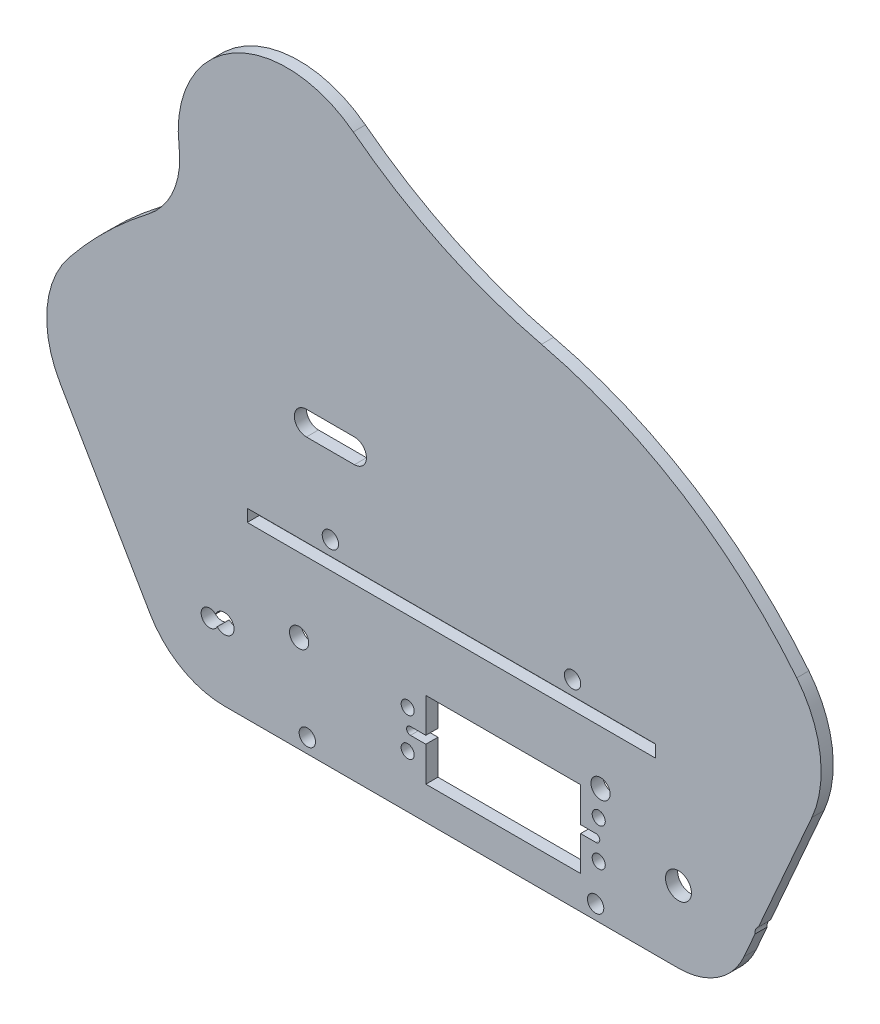
SolidWorks part; units mm, degrees
ref_plane "Front Plane" through (0, 0, 0) normal (0, 0, 1) x (1, 0, 0)
ref_plane "Top Plane" through (0, 0, 0) normal (0, 1, 0) x (1, 0, 0)
ref_plane "Right Plane" through (0, 0, 0) normal (1, 0, 0) x (0, 0, -1)
sketch "Sketch1" plane through (0, 0, 0) normal (0, 0, 1) x (1, 0, 0)
  line L8 (0, 18.9078) -> (120.015, 18.9078) construction
  line L18 (155.2575, 52.1157) -> (-50.9787, 52.1157) construction
  line L37 (0, 0) -> (120.015, 0)
  line L42 (19.7347, 25.5664) -> (0, 18.9078) construction
  line L55 (60.0075, 18.9078) -> (60.0075, 0) construction
  line L60 (137.3256, 11.3022) -> (120.015, 0) construction
  line L61 (-19.6481, 11.3022) -> (0, 0) construction
  line L62 (155.2575, 52.1157) -> (137.3256, 11.3022)
  line L63 (-43.3855, 52.1157) -> (-19.6481, 11.3022)
  line L64 (155.2575, 52.1157) -> (-43.3855, 52.1157) construction
  line L65 (137.3256, 11.3022) -> (-19.6481, 11.3022) construction
  line L66 (120.015, 18.9078) -> (99.4008, 30.8094) construction
  line L67 (151.2687, 82.096) -> (-41.1067, 82.096) construction
  circle A21 centre (120.015, 18.9078) radius 3.429
  circle A22 centre (0, 18.9078) radius 2.54
  arc A25 (137.3256, 11.3022) -> (120.015, 0) centre (120.015, 18.9078) cw
  circle A27 centre (19.7347, 25.5664) radius 2.54
  arc A34 (-19.6481, 11.3022) -> (0, 0) centre (0, 22.7296) ccw
  arc A36 (151.2687, 82.096) -> (155.2575, 52.1157) centre (128.6061, 63.8253) cw
  arc A37 (-41.1067, 82.096) -> (-43.3855, 52.1157) centre (-20.4591, 65.4498) ccw
  circle A38 centre (99.4008, 30.8094) radius 2.54
  arc A39 (151.2687, 82.096) -> (-41.1067, 82.096) centre (55.081, 4.5491) ccw
  dimension "D5" = 18.9078
  dimension "D8" = 59.818
  dimension "D3" = 20.6736
  dimension "D11" = 52.1157
  dimension "D13" = 30
  dimension "D10" = 5.08
  dimension "D15" = 123.554
  dimension "D16" = 6.858
  dimension "D4" = 18.645
  dimension "D6" = 20.8278
  dimension "D7" = 120.015
  dimension "D9" = 29.9803
  dimension "D12" = 52.1157
  dimension "D14" = 23.8032
extrude "Boss-Extrude1" add sketch "Sketch1" along normal blind 3.2004
sketch "Sketch2" plane through (0, 0, 0) normal (0, 0, -1) x (-1, 0, 0)
  line L0 (-60.0075, 52.1157) -> (-60.0075, 18.9078) construction
  line L1 (-155.2575, 52.1157) -> (50.9787, 52.1157) construction
  line L14 (0, 18.9078) -> (-120.015, 18.9078) construction
  line L15 (-60.0075, 7.62) -> (-60.0075, 0) construction
  line L28 (-92.0115, 52.1157) -> (-76.0095, 52.1157) construction
  line L29 (-76.0095, 52.1157) -> (-44.0055, 52.1157) construction
  line L30 (-44.0055, 52.1157) -> (-28.0035, 52.1157) construction
  line L31 (-98.1075, 3.81) -> (-21.9075, 3.81) construction
  line L32 (0, 0) -> (-120.015, 0) construction
  circle A0 centre (-92.0115, 52.1157) radius 2.159
  circle A3 centre (-28.0035, 52.1157) radius 2.159
  circle A4 centre (-98.1075, 3.81) radius 2.159
  circle A6 centre (-21.9075, 3.81) radius 2.159
  point P11 (-36.0045, 52.1157)
  point P16 (-84.0105, 52.1157)
  point P17 (-60.0075, 3.81)
  dimension "D3" = 4.318
  dimension "D5" = 7.62
  dimension "D1" = 76.2
  dimension "D2" = 16.002
  dimension "D4" = 48.006
extrude "Cut-Extrude1" cut sketch "Sketch2" against normal blind 3.2004
sketch "Sketch5" plane through (0, 0, 0) normal (0, 0, -1) x (-1, 0, 0)
  line L0 (0, 18.9078) -> (-120.015, 18.9078) construction
  line L6 (-94.129, 29.0678) -> (-94.129, 8.7478)
  line L7 (-53.235, 29.0678) -> (-53.235, 8.7478)
  line L12 (-73.682, 29.0678) -> (-73.682, 8.7478) construction
  line L13 (-98.932, 13.9078) -> (-98.932, 23.9078) construction
  line L14 (-48.432, 13.9078) -> (-48.432, 23.9078) construction
  line L15 (-98.932, 18.9078) -> (-48.432, 18.9078) construction
  line L21 (-94.129, 8.7478) -> (-53.235, 8.7478)
  line L25 (-94.129, 29.0678) -> (-53.235, 29.0678)
  circle A0 centre (-98.932, 23.9078) radius 1.7272
  circle A1 centre (-48.432, 13.9078) radius 1.7272
  circle A2 centre (-48.432, 23.9078) radius 1.7272
  circle A3 centre (-98.932, 13.9078) radius 1.7272
  circle A8 centre (-120.015, 18.9078) radius 3.429 construction
  point P8 (-63.635, 18.9078)
  point P9 (-73.682, 18.9078)
  dimension "D2" = 3.4544
  dimension "D3" = 40.894
  dimension "D5" = 10.4
  dimension "D6" = 46.333
  dimension "D1" = 50.5
  dimension "D4" = 20.32
extrude "Cut-Extrude3" cut sketch "Sketch5" against normal through all
sketch "Sketch6" plane through (0, 0, 3.2004) normal (0, 0, 1) x (1, 0, 0)
  line L3 (98.932, 18.9078) -> (48.432, 18.9078) construction
  line L4 (49.171, 19.9238) -> (53.235, 19.9238)
  line L5 (49.171, 19.9238) -> (49.171, 17.8918) construction
  line L7 (49.171, 17.8918) -> (53.235, 17.8918)
  line L8 (53.235, 19.9238) -> (53.235, 17.8918)
  line L9 (94.129, 19.9238) -> (98.193, 19.9238)
  line L10 (94.129, 19.9238) -> (94.129, 17.8918)
  line L11 (94.129, 17.8918) -> (98.193, 17.8918)
  line L12 (98.193, 19.9238) -> (98.193, 17.8918) construction
  line L13 (53.235, 8.7478) -> (53.235, 29.0678) construction
  line L14 (94.129, 29.0678) -> (94.129, 8.7478) construction
  arc A6 (98.193, 19.9238) -> (98.193, 17.8918) centre (98.193, 18.9078) cw
  arc A7 (49.171, 19.9238) -> (49.171, 17.8918) centre (49.171, 18.9078) ccw
  point P22 (53.235, 18.9078)
  point P23 (94.129, 18.9078)
  dimension "D4" = 4.064
  dimension "D5" = 2.032
extrude "Cut-Extrude4" cut sketch "Sketch6" against normal up to surface (3.2004 mm away) up to face at (97.2048, 23.9078, 0)
sketch "Sketch10" plane through (0, 0, 0) normal (0, 0, -1) x (-1, 0, 0)
  line L0 (0, 0) -> (-120.015, 0) construction
  line L1 (-34.3535, 78.7857) -> (-21.6535, 78.7857)
  line L2 (-34.3535, 78.7857) -> (-34.3535, 72.4357) construction
  line L3 (-34.3535, 72.4357) -> (-21.6535, 72.4357)
  line L4 (-21.6535, 78.7857) -> (-21.6535, 72.4357) construction
  arc A0 (-21.6535, 78.7857) -> (-21.6535, 72.4357) centre (-21.6535, 75.6107) cw
  arc A1 (-34.3535, 78.7857) -> (-34.3535, 72.4357) centre (-34.3535, 75.6107) ccw
  circle A4 centre (-28.0035, 52.1157) radius 2.159 construction
  dimension "D3" = 20.32
  dimension "D4" = 6.35
  dimension "D1" = 12.7
  dimension "D2" = 6.35
extrude "Cut-Extrude8" cut sketch "Sketch10" against normal up to surface (3.2004 mm away) up to face at (73.682, 18.9078, 3.2004)
sketch "Sketch11" plane through (0, 0, 0) normal (0, 0, -1) x (-1, 0, 0)
  line L5 (-76.0095, 52.1157) -> (-44.0055, 52.1157) construction
  line L7 (-60.0075, 52.1157) -> (-60.0075, 48.3057) construction
  line L9 (-6.0325, 48.3057) -> (-113.9825, 48.3057)
  line L10 (-6.0325, 48.3057) -> (-6.0325, 45.0545)
  line L11 (-6.0325, 45.0545) -> (-113.9825, 45.0545)
  line L12 (-113.9825, 48.3057) -> (-113.9825, 45.0545)
  dimension "D1" = 107.95
  dimension "D2" = 3.81
  dimension "D5" = 3.2512
extrude "Cut-Extrude9" cut sketch "Sketch11" against normal up to surface (3.2004 mm away) up to face at (28.0035, 75.6107, 3.2004)
sketch "Sketch12" plane through (0, 0, 0) normal (0, 0, -1) x (-1, 0, 0)
  circle A0 centre (-142.479, 18.2241) radius 2.2479
  circle A1 centre (3.9143, 18.2241) radius 2.2479
  circle A3 centre (-142.479, 18.2241) radius 1.651 construction
  circle A4 centre (3.9143, 18.2241) radius 1.651 construction
  dimension "D1" = 4.4958
extrude "Cut-Extrude10" cut sketch "Sketch12" against normal up to surface (3.2004 mm away) up to face at (60.0075, 46.6801, 3.2004)
sketch "Sketch13" plane through (0, 0, 0) normal (0, 0, -1) x (-1, 0, 0)
  line L0 (-83.8046, 124.7179) -> (-34.0526, 148.4576) construction
  line L1 (-83.8046, 124.7179) -> (20.1056, 102.5928)
  line L2 (-83.8046, 124.7179) -> (-55.081, 82.096) construction
  line L3 (-151.2687, 82.096) -> (41.1067, 82.096) construction
  arc A0 (-83.8046, 124.7179) -> (-34.0526, 148.4576) centre (-114.4589, 252.964) ccw
  arc A1 (41.1067, 82.096) -> (-151.2687, 82.096) centre (-55.081, 4.5491) ccw construction
  arc A2 (-34.0526, 148.4576) -> (11.9851, 122.0607) centre (-16.5269, 125.6789) cw
  arc A3 (11.9851, 122.0607) -> (20.1056, 102.5928) centre (32.9907, 119.395) ccw
  dimension "D1" = 55.1256
  dimension "D2" = 56.023
  dimension "D3" = 106.2396
  dimension "D4" = 37.529
extrude "Boss-Extrude2" add sketch "Sketch13" against normal up to surface (3.2004 mm away) up to face at (74.0569, 37.0878, 3.2004)
